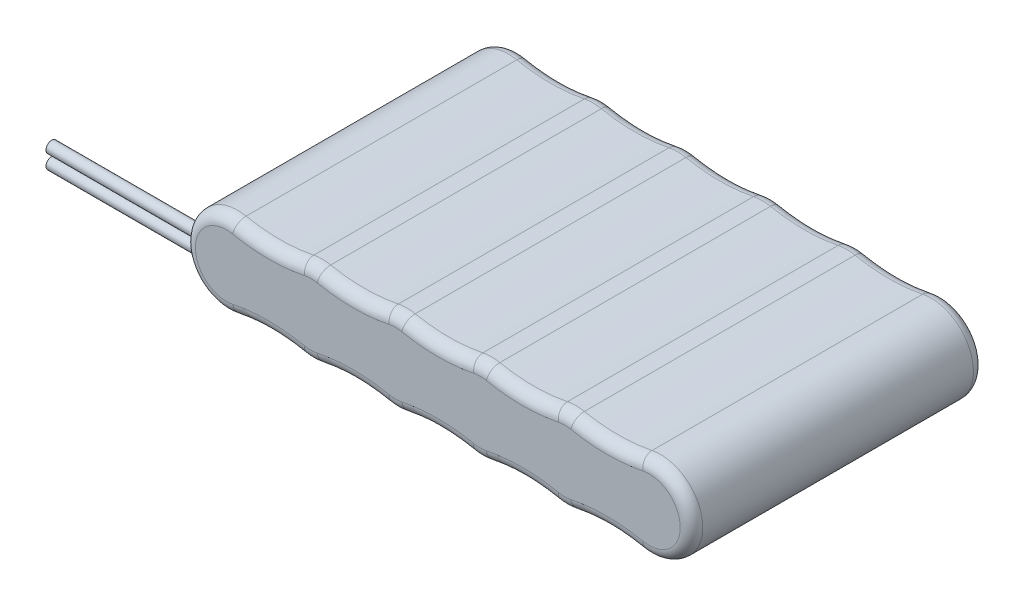
SolidWorks part; units mm, degrees
ref_plane "Plan de face" through (0, 0, 0) normal (0, 0, 1) x (1, 0, 0)
ref_plane "Plan de dessus" through (0, 0, 0) normal (0, 1, 0) x (1, 0, 0)
ref_plane "Plan de droite" through (0, 0, 0) normal (1, 0, 0) x (0, 0, -1)
sketch "Esquisse2" plane through (0, 0, 0) normal (0, 0, 1) x (1, 0, 0)
  line L0 (0, 0) -> (0, 36.7423) construction
  line L1 (7.5, 0) -> (-7.5, 0) construction
  line L2 (-7.5, 7.5) -> (7.5, 7.5) construction
  arc A0 (-6, 7.3485) -> (-6, -7.3485) centre (-7.5, 0) ccw
  arc A1 (6, -7.3485) -> (6, 7.3485) centre (7.5, 0) ccw
  arc A2 (-6, 7.3485) -> (6, 7.3485) centre (0, 36.7423) ccw
  arc A3 (-6, -7.3485) -> (6, -7.3485) centre (0, -36.7423) cw
  arc A4 (21, -7.3485) -> (21, 7.3485) centre (22.5, 0) ccw
  arc A5 (9, 7.3485) -> (21, 7.3485) centre (15, 36.7423) ccw
  arc A6 (9, 7.3485) -> (9, -7.3485) centre (7.5, 0) ccw
  arc A7 (9, -7.3485) -> (21, -7.3485) centre (15, -36.7423) cw
  arc A8 (36, -7.3485) -> (36, 7.3485) centre (37.5, 0) ccw
  arc A9 (24, 7.3485) -> (36, 7.3485) centre (30, 36.7423) ccw
  arc A10 (24, 7.3485) -> (24, -7.3485) centre (22.5, 0) ccw
  arc A11 (24, -7.3485) -> (36, -7.3485) centre (30, -36.7423) cw
  arc A12 (51, -7.3485) -> (51, 7.3485) centre (52.5, 0) ccw
  arc A13 (39, 7.3485) -> (51, 7.3485) centre (45, 36.7423) ccw
  arc A14 (39, 7.3485) -> (39, -7.3485) centre (37.5, 0) ccw
  arc A15 (39, -7.3485) -> (51, -7.3485) centre (45, -36.7423) cw
  arc A16 (66, -7.3485) -> (66, 7.3485) centre (67.5, 0) ccw
  arc A17 (54, 7.3485) -> (66, 7.3485) centre (60, 36.7423) ccw
  arc A18 (54, 7.3485) -> (54, -7.3485) centre (52.5, 0) ccw
  arc A19 (54, -7.3485) -> (66, -7.3485) centre (60, -36.7423) cw
  dimension "D1" = 15
  dimension "D2" = 15
  dimension "D3" = 30
  dimension "D5" = 15
  dimension "D4" = 5
extrude "Boss.-Extru.1" add sketch "Esquisse2" along normal blind 52 contours A6 A2 A0 A3 | A1 A6 | A10 A5 A1 | A10 A1 A7 | A4 A10 | A14 A9 A4 | A14 A4 A11 | A8 A14 | A18 A13 A8 | A18 A8 A15 | A12 A18 | A12 A19 A16 A17
fillet "Congé1" radius 2 40 edges at (60, -6.7423, 0) (60, -6.7423, 52) (52.5, 7.5, 0) (52.5, 7.5, 52) (45, -6.7423, 0) (45, -6.7423, 52) (37.5, 7.5, 0) (37.5, 7.5, 52) (30, -6.7423, 0) (30, -6.7423, 52) (22.5, 7.5, 0) (22.5, 7.5, 52) (15, -6.7423, 0) (15, -6.7423, 52) (7.5, -7.5, 0) (7.5, -7.5, 52) (0, -6.7423, 0) (0, -6.7423, 52) (-15, 0, 0) (-15, 0, 52) (0, 6.7423, 0) (0, 6.7423, 52) (7.5, 7.5, 0) (7.5, 7.5, 52) (15, 6.7423, 0) (15, 6.7423, 52) (22.5, -7.5, 0) (22.5, -7.5, 52) (30, 6.7423, 0) (30, 6.7423, 52) (37.5, -7.5, 0) (37.5, -7.5, 52) (45, 6.7423, 0) (45, 6.7423, 52) (52.5, -7.5, 0) (52.5, -7.5, 52) (60, 6.7423, 0) (60, 6.7423, 52) (75, 0, 0) (75, 0, 52)
sketch "Esquisse3" plane through (0, 0, 0) normal (1, 0, 0) x (0, 0, -1)
  line L0 (0, 0) -> (-52, 0) construction
  line L1 (0, -5.5) -> (0, 5.5) construction
  line L2 (-52, 5.5) -> (-52, -5.5) construction
  line L3 (-50.5, 1.25) -> (-50.5, -1.25) construction
  line L4 (-52, 5.5) -> (-52, -5.5) construction
  circle A0 centre (-50.5, 1.25) radius 1
  circle A1 centre (-50.5, -1.25) radius 1
  point P8 (-50.5, 0)
  dimension "D1" = 2
  dimension "D2" = 2
  dimension "D3" = 2.5
  dimension "D4" = 1.5
extrude "Boss.-Extru.2" add sketch "Esquisse3" against normal blind 40
